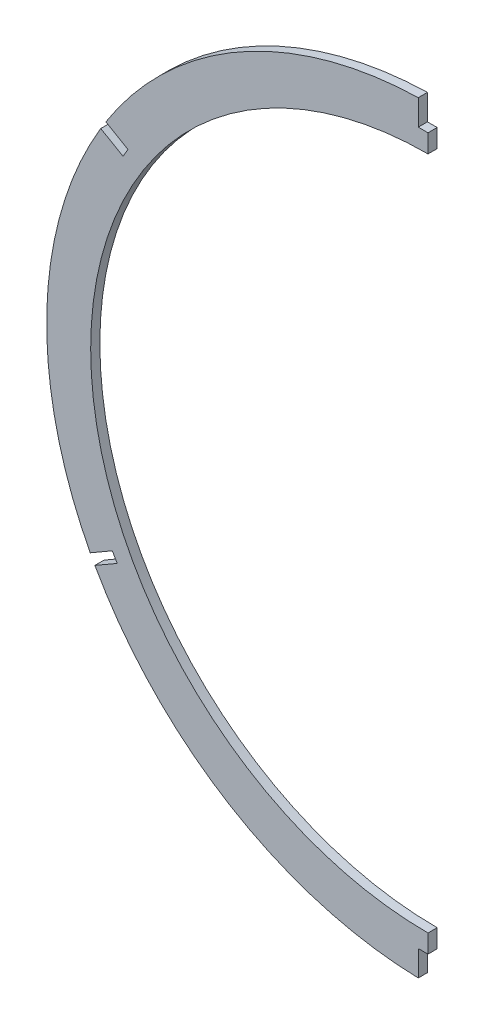
SolidWorks part; units mm, degrees
material "Plywood"
ref_plane "Front Plane" through (0, 0, 0) normal (0, 0, 1) x (1, 0, 0)
ref_plane "Top Plane" through (0, 0, 0) normal (0, 1, 0) x (1, 0, 0)
ref_plane "Right Plane" through (0, 0, 0) normal (1, 0, 0) x (0, 0, -1)
sketch "Sketch2" plane through (0, 0, 0) normal (0, 0, 1) x (1, 0, 0)
  line L0 (0, 0) -> (0, 236.6718) construction
  line L1 (-1.651, 128.5137) -> (-1.651, 121.4017) construction
  line L3 (1.651, 128.5137) -> (1.651, 121.4017) construction
  line L4 (-1.651, 121.4017) -> (1.651, 121.4017) construction
  line L5 (-136.2041, -77.9016) -> (0, 0.7359) construction
  line L6 (-136.2041, -77.9016) -> (0, 0.7359) construction
  line L7 (136.2041, -77.9016) -> (0, 0.7359) construction
  line L8 (136.2041, -77.9016) -> (0, 0.7359) construction
  line L9 (-116.9741, -64.8927) -> (-110.0155, -60.8752) construction
  line L10 (-115.4036, -67.7988) -> (-108.3645, -63.7348) construction
  line L11 (-110.0155, -60.8752) -> (-108.3645, -63.7348) construction
  line L12 (-117.55, -65.2252) -> (-116.9741, -64.8927) construction
  line L13 (-115.899, -68.0849) -> (-115.4036, -67.7988) construction
  line L14 (115.4036, -67.7988) -> (109.2442, -64.2427) construction
  line L15 (110.8952, -61.3831) -> (109.2442, -64.2427) construction
  line L16 (116.9741, -64.8927) -> (110.8952, -61.3831) construction
  arc A0 (-1.651, 128.5137) -> (-116.9741, -64.8927) centre (0, -3.556) ccw
  arc A1 (0.0665, 128.1531) -> (63.0696, -118.8475) centre (0, -3.3993) ccw construction
  circle A2 centre (0, -3.556) radius 116.84
  arc A3 (63.0696, -118.8475) -> (0.0665, 128.1531) centre (0, -3.3993) ccw construction
  arc A4 (0, 128.524) -> (-1.651, 128.5137) centre (0, -3.556) ccw
  circle A5 centre (0, -3.556) radius 132.08 construction
  arc A6 (1.651, 128.5137) -> (0, 128.524) centre (0, -3.556) ccw
  arc A7 (-116.9741, -64.8927) -> (-116.1978, -66.3509) centre (0, -3.556) ccw
  arc A8 (-115.4036, -67.7988) -> (115.4036, -67.7988) centre (0, -3.556) ccw
  arc A9 (-116.1978, -66.3509) -> (-115.4036, -67.7988) centre (0, -3.556) ccw
  arc A10 (115.4036, -67.7988) -> (116.1978, -66.3509) centre (0, -3.556) ccw
  arc A11 (116.9741, -64.8927) -> (1.651, 128.5137) centre (0, -3.556) ccw
  arc A12 (116.1978, -66.3509) -> (116.9741, -64.8927) centre (0, -3.556) ccw
  point P24 (-115.4036, -67.7988)
  dimension "D1" = 3.556
  dimension "D3" = 264.16
  dimension "D2" = 15.24
  dimension "D4" = 3.302
  dimension "D5" = 7.112
  dimension "D6" = 3.302
  dimension "D7" = 8.128
  dimension "D8" = 7.076
extrude "Boss-Extrude1" add sketch "Sketch2" along normal mid plane 3.175
sketch "Sketch3" plane through (0, 0, 0) normal (1, 0, 0) x (0, 0, -1)
  line L1 (-109.3908, 192.564) -> (122.8198, 192.564)
  line L2 (-109.3908, 192.564) -> (-109.3908, -206.3906)
  line L3 (-109.3908, -206.3906) -> (122.8198, -206.3906)
  line L4 (122.8198, 192.564) -> (122.8198, -206.3906)
extrude "Cut-Extrude1" cut sketch "Sketch3" along normal through all
sketch "Sketch4" plane through (0, 0, 1.5875) normal (0, 0, 1) x (1, 0, 0)
  line L0 (0, 0) -> (0, 113.284) construction
  line L1 (0, 113.284) -> (0, 119.634) construction
  line L2 (-99.2768, 58.0533) -> (-104.776, 61.2283) construction
  line L3 (0, 119.634) -> (-3.3782, 119.634)
  line L4 (0, 119.634) -> (0, 129.794)
  line L5 (0, 129.794) -> (-3.3782, 129.794)
  line L6 (-3.3782, 119.634) -> (-3.3782, 129.794)
  line L7 (-105.6206, 59.7655) -> (-103.9315, 62.6911)
  line L8 (0, 0.7359) -> (-7.6459, 0.7359) construction
  line L9 (-103.9315, 62.6911) -> (-112.7303, 67.7711)
  line L11 (-130.6719, 76.1793) -> (0, 0.7359) construction
  line L12 (-112.7303, 67.7711) -> (-114.4194, 64.8455)
  line L13 (-130.6719, -74.7076) -> (0, 0.7359) construction
  line L14 (0, 0.7359) -> (0, -120.396) construction
  line L15 (0, -120.396) -> (0, -126.746) construction
  line L16 (0, -135.636) -> (0, -120.396) construction
  line L17 (-102.9936, -58.7275) -> (-108.4929, -61.9025) construction
  line L18 (0, -126.746) -> (-3.3782, -126.746)
  line L19 (0, -126.746) -> (0, -136.906)
  line L20 (0, -136.906) -> (-3.3782, -136.906)
  line L21 (-3.3782, -126.746) -> (-3.3782, -136.906)
  line L22 (-107.6483, -63.3653) -> (-109.3374, -60.4397)
  line L23 (-109.3374, -60.4397) -> (-118.1363, -65.5197)
  line L24 (-118.1363, -65.5197) -> (-116.4472, -68.4453)
  line L25 (-107.6483, -63.3653) -> (-116.4472, -68.4453)
  line L26 (-105.6206, 59.7655) -> (-114.4194, 64.8455)
  point P18 (-102.9936, -58.7275)
  point P23 (-99.2768, 58.0533)
  point P30 (-117.2917, -66.9825)
  point P32 (-113.5748, 66.3083)
  dimension "D1" = 113.284
  dimension "D2" = 6.35
  dimension "D3" = 10.16
  dimension "D4" = 3.3782
  dimension "D5" = 0.7359
  dimension "D6" = 60
  dimension "D7" = 121.1319
  dimension "D8" = 6.35
  dimension "D9" = 10.16
  dimension "D10" = 3.3782
  dimension "D11" = 118.9268
  dimension "D12" = 6.35
  dimension "D13" = 10.16
  dimension "D14" = 1.6891
  dimension "D15" = 114.6349
  dimension "D16" = 6.35
  dimension "D17" = 1.6891
  dimension "D18" = 10.16
extrude "Cut-Extrude2" cut sketch "Sketch4" against normal through all
